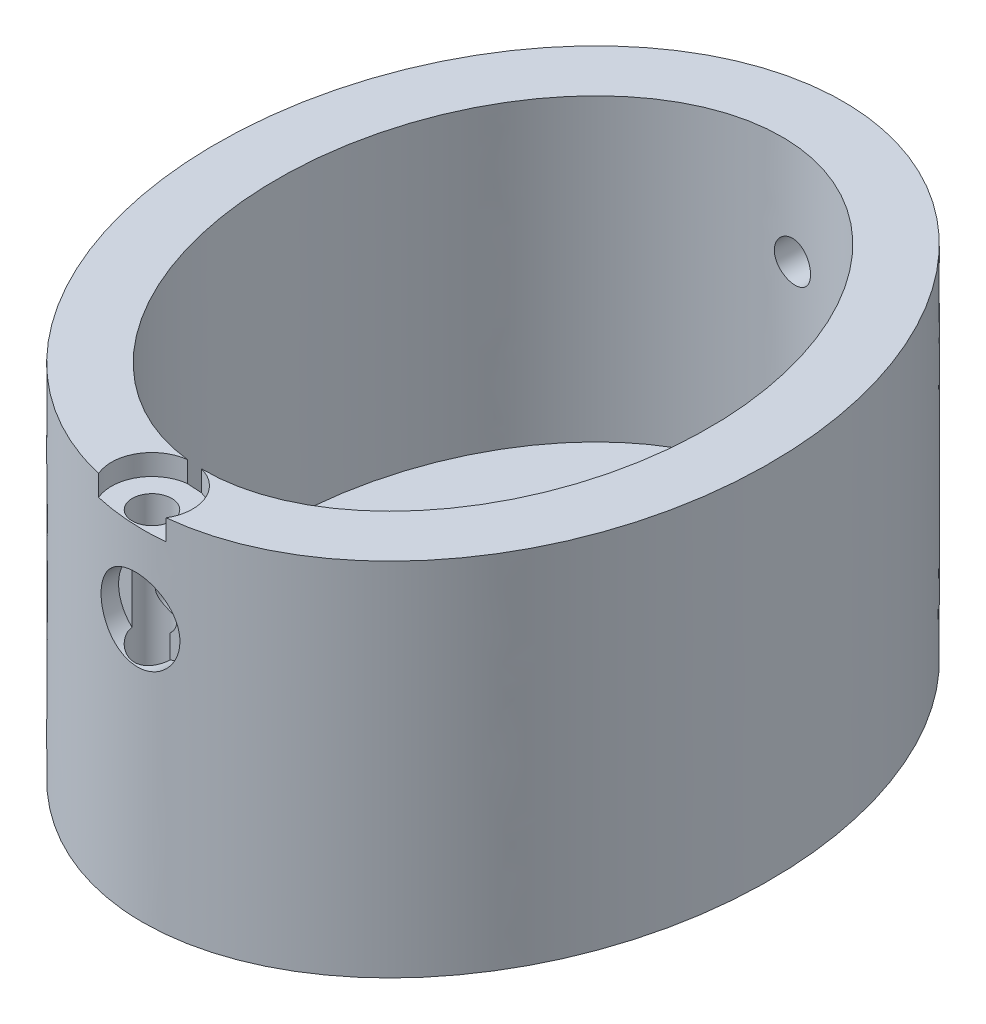
SolidWorks part; units mm, degrees
ref_plane "Front Plane" through (0, 0, 0) normal (0, 0, 1) x (1, 0, 0)
ref_plane "Top Plane" through (0, 0, 0) normal (0, 1, 0) x (1, 0, 0)
ref_plane "Right Plane" through (0, 0, 0) normal (1, 0, 0) x (0, 0, -1)
sketch "Sketch1" plane through (0, 0, 0) normal (0, 1, 0) x (1, 0, 0)
  ellipse E0 centre (0, 0) end of major axis (0, -29.0722) minor radius 22.9874
  dimension "D1" = 22.9874
extrude "Boss-Extrude1" add sketch "Sketch1" along normal blind 29.972
shell "Shell1" thickness 5.08
hole_wizard "CBORE for #4 Binding Head Machine Screw1" positions "Sketch3" profile "Sketch4" counterbore size "#4" standard "ANSI Inch" end condition through all
sketch "Sketch3" plane through (0, 29.972, 0) normal (0, 1, 0) x (1, 0, 0)
  point P0 (-1.0602, -27.256)
sketch "Sketch4" plane through (-1.0602, 29.972, 27.256) normal (1, 0, 0) x (0, 0, 1)
  line L0 (0, 0) -> (0, 29.972)
  line L1 (0, 29.972) -> (1.6319, 29.972)
  line L3 (1.6319, 29.972) -> (1.632, 1.7272)
  line L4 (1.632, 1.7272) -> (3.3731, 1.7272)
  line L5 (3.3731, 1.7272) -> (3.3731, 0)
  line L7 (3.3731, 0) -> (0, 0)
  line L11 (0, -6.35) -> (0, 107.95) construction
  dimension "Thru Hole Dia." = 3.2639
  dimension "Thru Hole Depth" = 29.972
  dimension "C'Bore Dia." = 6.7462
  dimension "C'Bore Depth" = 1.7272
hole_wizard "CBORE for #4 Binding Head Machine Screw2" positions "3DSketch1" profile "Sketch5" counterbore size "#4" standard "ANSI Inch" end condition through all
sketch3d "3DSketch1"
  point P0 (-0.5301, 21.5136, 29.0645)
sketch "Sketch5" plane through (-0.5301, 21.5136, 29.0645) normal (0, 1, 0) x (0.9996, 0, 0.0292)
  line L0 (0, 0) -> (0, 58.7978)
  line L1 (0, 58.7978) -> (1.6319, 58.7978)
  line L3 (1.6319, 58.7978) -> (1.632, 1.7272)
  line L4 (1.632, 1.7272) -> (3.3731, 1.7272)
  line L5 (3.3731, 1.7272) -> (3.3731, 0)
  line L7 (3.3731, 0) -> (0, 0)
  line L11 (0, -6.35) -> (0, 107.95) construction
  dimension "Thru Hole Dia." = 3.2639
  dimension "Thru Hole Depth" = 58.7978
  dimension "C'Bore Dia." = 6.7462
  dimension "C'Bore Depth" = 1.7272
